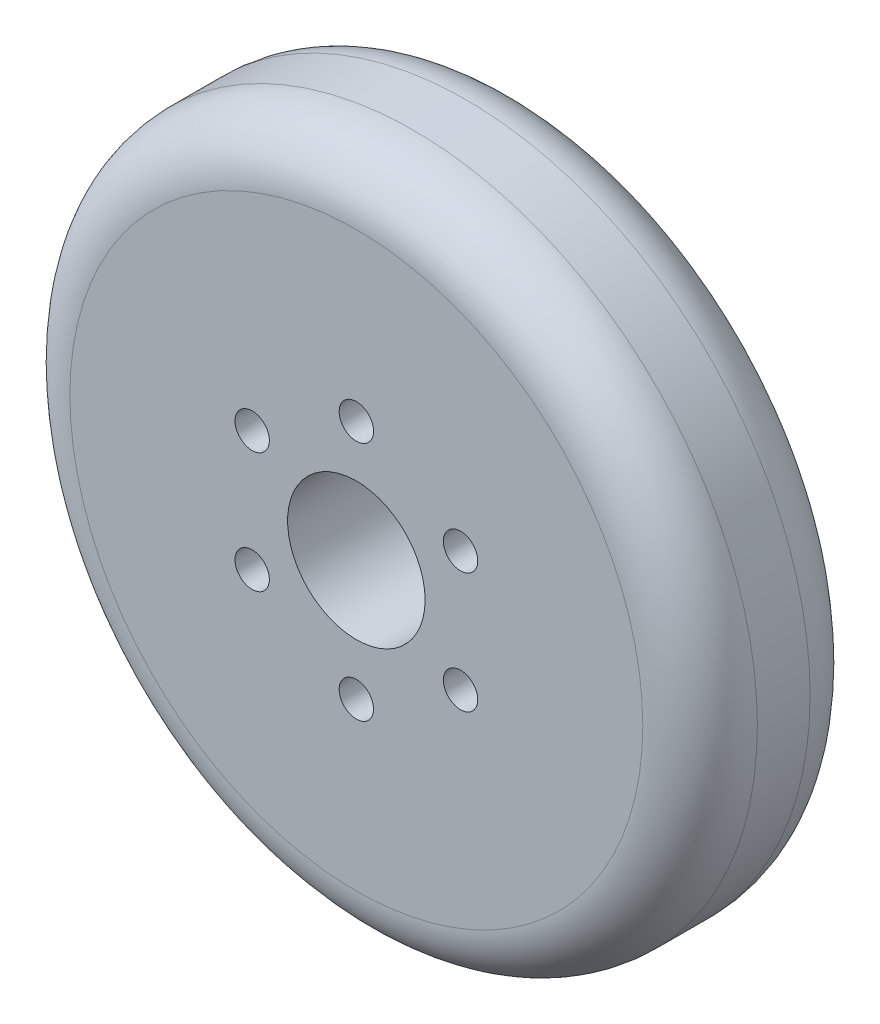
SolidWorks part; units mm, degrees
ref_plane "正面" through (0, 0, 0) normal (0, 0, 1) x (1, 0, 0)
ref_plane "平面" through (0, 0, 0) normal (0, 1, 0) x (1, 0, 0)
ref_plane "右側面" through (0, 0, 0) normal (1, 0, 0) x (0, 0, -1)
sketch "ｽｹｯﾁ1" plane through (0, 0, 0) normal (0, 0, 1) x (1, 0, 0)
  line L0 (0, 0) -> (0, 10.5) construction
  circle A0 centre (0, 0) radius 30
  circle A1 centre (0, 0) radius 6
  circle A2 centre (0, 10.5) radius 1.5 construction
  circle A3 centre (0, 0) radius 10.5 construction
  dimension "D1" = 60
  dimension "D2" = 12
  dimension "D3" = 21
  dimension "D4" = 3
extrude "ﾎﾞｽ - 押し出し1" add sketch "ｽｹｯﾁ1" along normal blind 14.6
fillet "ﾌｨﾚｯﾄ2" radius 5 2 edges at (30, 0, 14.6) (30, 0, 0)
sketch "ｽｹｯﾁ3" plane through (0, 0, 0) normal (0, 0, -1) x (-1, 0, 0)
  circle A0 centre (0, 0) radius 10.5 construction
  circle A1 centre (0, 10.5) radius 1.5
  dimension "D1" = 21
  dimension "D2" = 3
extrude "ｶｯﾄ - 押し出し1" cut sketch "ｽｹｯﾁ3" against normal through all
pattern_circular "円形ﾊﾟﾀｰﾝ2" count 6 over 360 about axis through (0, 0, 0) along (0, 0, 1) of "ｶｯﾄ - 押し出し1"
